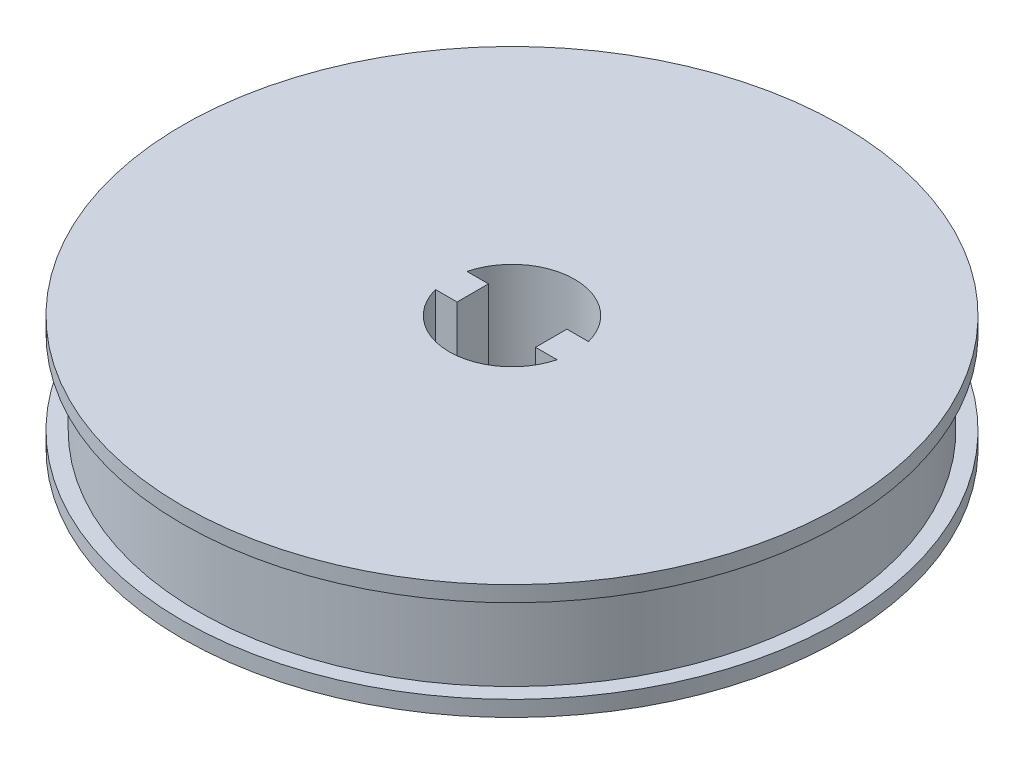
SolidWorks part; units mm, degrees
ref_plane "Plan de face" through (0, 0, 0) normal (0, 0, 1) x (1, 0, 0)
ref_plane "Plan de dessus" through (0, 0, 0) normal (0, 1, 0) x (1, 0, 0)
ref_plane "Plan de droite" through (0, 0, 0) normal (1, 0, 0) x (0, 0, -1)
sketch "Esquisse2" plane through (0, 0, 0) normal (0, 0, 1) x (1, 0, 0)
  line L0 (6, 5.3653) -> (6, -5.6347)
  line L1 (6, 5.3653) -> (31.5, 5.3653)
  line L2 (31.5, 5.3653) -> (31.5, 3.8653)
  line L3 (31.5, 3.8653) -> (30, 3.8653)
  line L4 (31.5, -5.6347) -> (6, -5.6347)
  line L5 (0, 0) -> (0, 15.5979) construction
  line L6 (30, 3.8653) -> (30, -4.1347)
  line L7 (30, -4.1347) -> (31.5, -4.1347)
  line L8 (31.5, -4.1347) -> (31.5, -5.6347)
  dimension "D1" = 6
  dimension "D2" = 1.5
  dimension "D3" = 11
  dimension "D5" = 1.5
  dimension "D6" = 8
  dimension "D7" = 1.5
  dimension "D8" = 1.5
  dimension "D9" = 30
revolve "Révolution1" add sketch "Esquisse2" angle 360 about L5
sketch "Esquisse6" plane through (0, 5.3653, 0) normal (0, 1, 0) x (1, 0, 0)
  line L0 (0, 0) -> (0, -8.5771) construction
  line L1 (-8.25, -1.5) -> (-3.75, -1.5)
  line L2 (-6, 0) -> (13.3406, 0) construction
  line L3 (-8.25, -1.5) -> (-8.25, 1.5)
  line L4 (-8.25, 1.5) -> (-3.75, 1.5)
  line L5 (-3.75, -1.5) -> (-3.75, 1.5)
  line L6 (-8.25, -1.5) -> (-3.75, 1.5) construction
  line L7 (-8.25, 1.5) -> (-3.75, -1.5) construction
  line L8 (8.25, -1.5) -> (3.75, 1.5) construction
  line L9 (3.75, -1.5) -> (3.75, 1.5)
  line L10 (8.25, 1.5) -> (3.75, 1.5)
  line L11 (8.25, 1.5) -> (3.75, -1.5) construction
  line L12 (8.25, -1.5) -> (8.25, 1.5)
  line L13 (8.25, -1.5) -> (3.75, -1.5)
  circle A0 centre (0, 0) radius 6 construction
  point P3 (-6, 0)
  point P17 (6, 0)
  dimension "D1" = 3
  dimension "D2" = 2.25
  dimension "D3" = 6
  dimension "D4" = 6
extrude "Boss.-Extru.1" add sketch "Esquisse6" against normal blind 11
